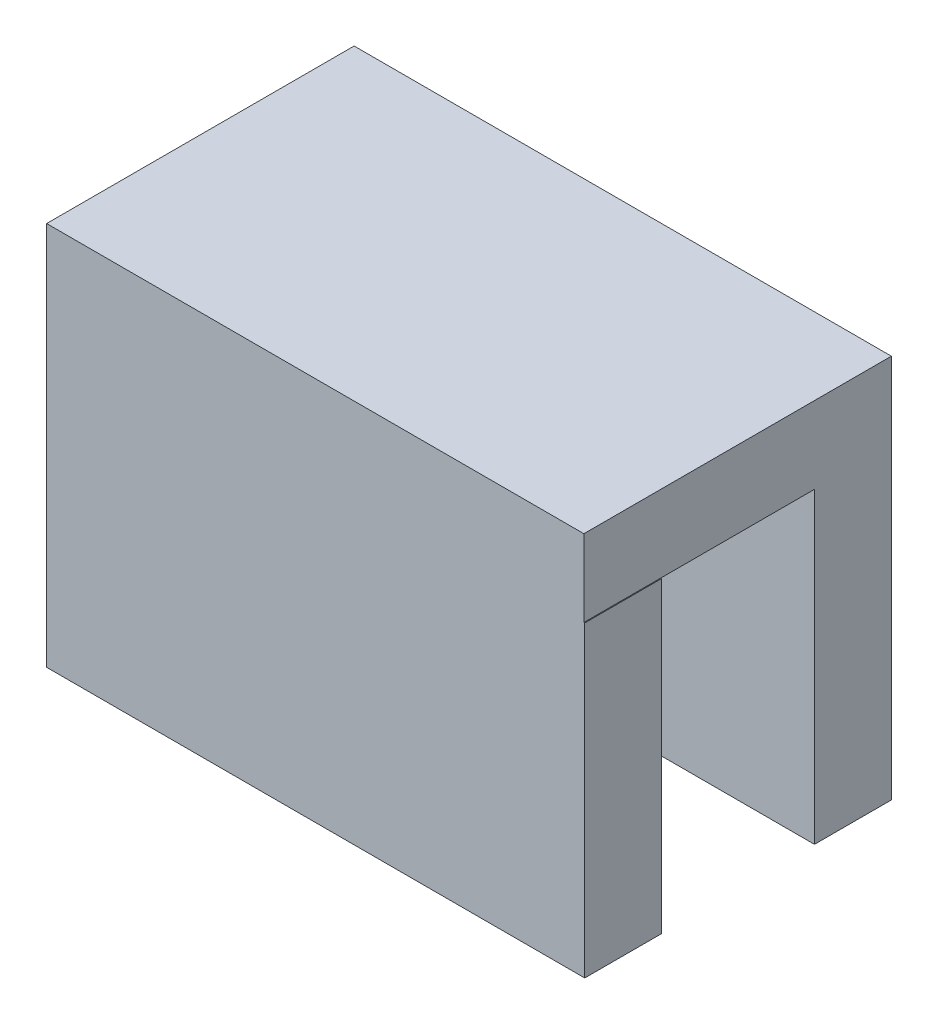
SolidWorks part; units mm, degrees
ref_plane "Front Plane" through (0, 0, 0) normal (0, 0, 1) x (1, 0, 0)
ref_plane "Top Plane" through (0, 0, 0) normal (0, 1, 0) x (1, 0, 0)
ref_plane "Right Plane" through (0, 0, 0) normal (1, 0, 0) x (0, 0, -1)
sketch "Sketch1" plane through (0, 0, 0) normal (0, 0, 1) x (1, 0, 0)
  line L1 (0, 0) -> (19.05, 0)
  line L2 (0, 0) -> (0, 12.7)
  line L3 (0, 12.7) -> (19.05, 12.7)
  line L4 (19.05, 0) -> (19.05, 12.7)
  dimension "D1" = 12.7
  dimension "D2" = 19.05
extrude "Boss-Extrude1" add sketch "Sketch1" along normal blind 3.175
sketch "Sketch3" plane through (0, 12.7, 0) normal (0, 1, 0) x (1, 0, 0)
  line L1 (0, -3.175) -> (19.0146, -3.175)
  line L2 (0, -3.175) -> (0, 9.525)
  line L3 (0, 9.525) -> (19.0146, 9.525)
  line L4 (19.0146, -3.175) -> (19.0146, 9.525)
  dimension "D1" = 12.7
extrude "Boss-Extrude2" add sketch "Sketch3" along normal blind 3.175
sketch "Sketch4" plane through (0, 12.7, 0) normal (0, -1, 0) x (1, 0, 0)
  line L0 (19.0146, 0) -> (19.0146, -9.525) construction
  line L1 (0, -9.525) -> (19.0146, -9.525)
  line L2 (0, -9.525) -> (0, -6.35)
  line L3 (0, -6.35) -> (19.0146, -6.35)
  line L4 (19.0146, -9.525) -> (19.0146, -6.35)
  dimension "D1" = 3.175
sketch "Sketch5" plane through (0, 0, 0) normal (-1, 0, 0) x (0, 0, 1)
  line L0 (3.175, 15.875) -> (3.175, 0) construction
  line L1 (-9.525, 15.875) -> (3.175, 15.875)
  line L2 (-9.525, 15.875) -> (-9.525, 0)
  line L3 (-9.525, 0) -> (3.175, 0)
  line L4 (3.175, 15.875) -> (3.175, 0)
extrude "Boss-Extrude4" add sketch "Sketch5" along normal blind 3.175
sketch "Sketch6" plane through (-3.175, 0, 0) normal (-1, 0, 0) x (0, 0, 1)
  line L0 (-3.175, 15.875) -> (-3.175, 0) construction
  line L1 (3.175, 15.875) -> (-9.525, 15.875) construction
  line L2 (-9.525, 0) -> (3.175, 0) construction
  line L3 (-9.525, 5.08) -> (3.175, 5.08) construction
  line L4 (-9.525, 15.875) -> (-9.525, 0) construction
  line L5 (3.175, 0) -> (3.175, 15.875) construction
  circle A0 centre (-3.175, 5.08) radius 2.54
  dimension "D2" = 5.08
  dimension "D1" = 5.08
extrude "Cut-Extrude1" cut sketch "Sketch6" against normal through all
extrude "Boss-Extrude5" add sketch "Sketch4" along normal blind 12.7
